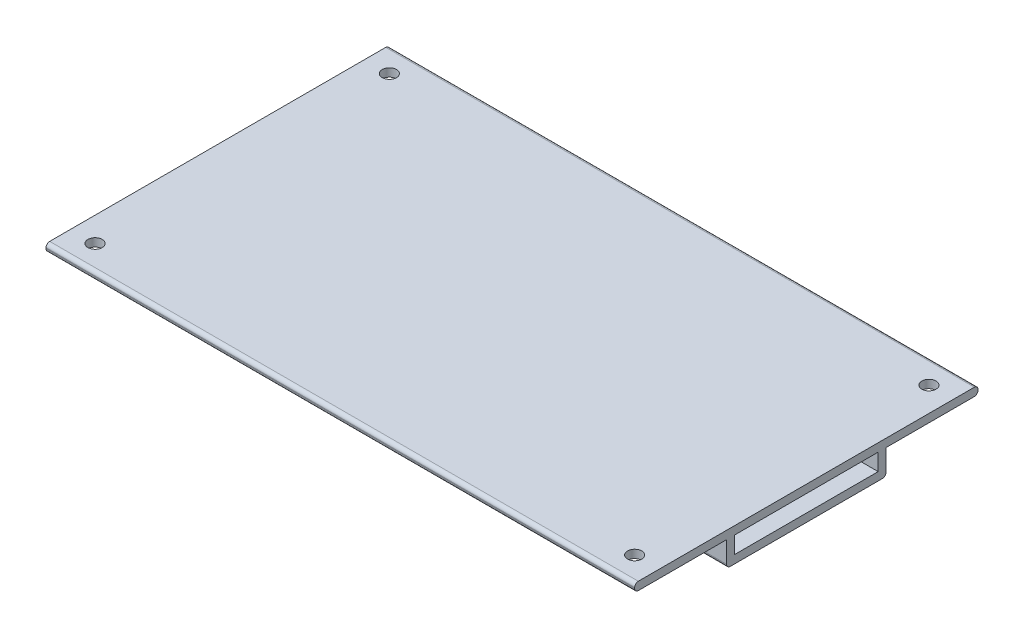
SolidWorks part; units mm, degrees
material "6061 Alloy"
ref_plane "Front Plane" through (0, 0, 0) normal (0, 0, 1) x (1, 0, 0)
ref_plane "Top Plane" through (0, 0, 0) normal (0, 1, 0) x (1, 0, 0)
ref_plane "Right Plane" through (0, 0, 0) normal (1, 0, 0) x (0, 0, -1)
sketch "Sketch1" plane through (0, 0, 0) normal (1, 0, 0) x (0, 0, -1)
  line L0 (-16.25, 0) -> (-16.25, 5.1)
  line L1 (-16.25, 5.1) -> (-35, 5.1)
  line L2 (-35, 5.1) -> (-35, 6.76)
  line L3 (-35, 6.76) -> (35, 6.76)
  line L4 (35, 6.76) -> (35, 5.1)
  line L5 (35, 5.1) -> (16.25, 5.1)
  line L6 (16.25, 5.1) -> (16.25, 0)
  line L7 (16.25, 0) -> (-16.25, 0)
  line L9 (-14.65, 5.1) -> (14.65, 5.1)
  line L10 (-14.65, 5.1) -> (-14.65, 1.66)
  line L11 (-14.65, 1.66) -> (14.65, 1.66)
  line L12 (14.65, 5.1) -> (14.65, 1.66)
  line L13 (-14.65, 5.1) -> (14.65, 1.66) construction
  line L14 (-14.65, 1.66) -> (14.65, 5.1) construction
  point P2 (0, 0)
  point P9 (0, 6.76)
  point P11 (0, 3.38)
  dimension "D1" = 70
  dimension "D2" = 1.66
  dimension "D3" = 5.1
  dimension "D4" = 32.5
  dimension "D5" = 1.66
  dimension "D6" = 1.6
extrude "Boss-Extrude1" add sketch "Sketch1" along normal blind 120
fillet "Fillet1" radius 0.75 6 edges at (60, 0, -16.25) (60, 0, 16.25) (60, 5.1, -35) (60, 6.76, -35) (60, 5.1, 35) (60, 6.76, 35)
sketch "Sketch2" plane through (0, 6.76, 0) normal (0, 1, 0) x (1, 0, 0)
  line L0 (120, 34.25) -> (120, -34.25) construction
  line L2 (0, 0) -> (120, 0) construction
  line L4 (0, 35) -> (120, 35) construction
  circle A0 centre (115, 30) radius 1.45
  circle A1 centre (5, 30) radius 1.45
  circle A2 centre (5, -30) radius 1.45
  circle A3 centre (115, -30) radius 1.45
  point P11 (60, 35)
  dimension "D3" = 2.9
  dimension "D6" = 2.9
  dimension "D4" = 55
  dimension "D1" = 55
  dimension "D2" = 30
  dimension "D5" = 30
extrude "Cut-Extrude1" cut sketch "Sketch2" against normal up to next
